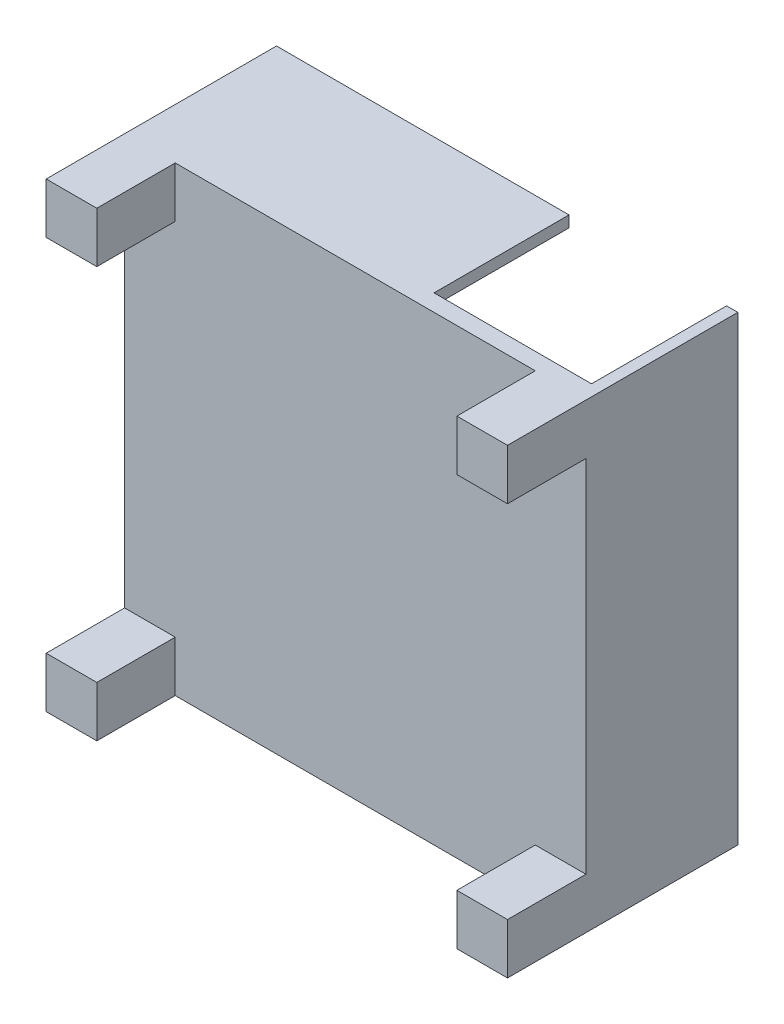
SolidWorks part; units mm, degrees
ref_plane "Piano frontale" through (0, 0, 0) normal (0, 0, 1) x (1, 0, 0)
ref_plane "Piano superiore" through (0, 0, 0) normal (0, 1, 0) x (1, 0, 0)
ref_plane "Piano destro" through (0, 0, 0) normal (1, 0, 0) x (0, 0, -1)
sketch "Schizzo1" plane through (0, 0, 0) normal (0, 0, 1) x (1, 0, 0)
  line L1 (0, 0) -> (41, 0)
  line L2 (0, 0) -> (0, 41)
  line L3 (0, 41) -> (41, 41)
  line L4 (41, 0) -> (41, 41)
  dimension "D1" = 41
  dimension "D2" = 41
extrude "Estrusione-Estrusione1" add sketch "Schizzo1" along normal blind 1.5 contours L1 L4 L3 L2
sketch "Schizzo5" plane through (0, 0, 1.5) normal (0, 0, 1) x (1, 0, 0)
  line L1 (0, 0) -> (4.5, 0)
  line L2 (0, 0) -> (0, 4.5)
  line L3 (0, 4.5) -> (4.5, 4.5)
  line L4 (4.5, 0) -> (4.5, 4.5)
  dimension "D1" = 4.5
  dimension "D2" = 4.5
extrude "Estrusione-Estrusione2" add sketch "Schizzo5" along normal blind 6.97
sketch "Schizzo6" plane through (0, 0, 1.5) normal (0, 0, 1) x (1, 0, 0)
  line L1 (41, 0) -> (36.5, 0)
  line L2 (41, 0) -> (41, 4.5)
  line L3 (41, 4.5) -> (36.5, 4.5)
  line L4 (36.5, 0) -> (36.5, 4.5)
  dimension "D1" = 4.5
  dimension "D2" = 4.5
extrude "Estrusione-Estrusione3" add sketch "Schizzo6" along normal blind 6.97
sketch "Schizzo7" plane through (0, 0, 1.5) normal (0, 0, 1) x (1, 0, 0)
  line L1 (0, 41) -> (4.5, 41)
  line L2 (0, 41) -> (0, 36.5)
  line L3 (0, 36.5) -> (4.5, 36.5)
  line L4 (4.5, 41) -> (4.5, 36.5)
  dimension "D1" = 4.5
  dimension "D2" = 4.5
extrude "Estrusione-Estrusione4" add sketch "Schizzo7" along normal blind 6.97
sketch "Schizzo8" plane through (0, 0, 1.5) normal (0, 0, 1) x (1, 0, 0)
  line L1 (41, 41) -> (36.5, 41)
  line L2 (41, 41) -> (41, 36.5)
  line L3 (41, 36.5) -> (36.5, 36.5)
  line L4 (36.5, 41) -> (36.5, 36.5)
  dimension "D1" = 4.5
  dimension "D2" = 4.5
extrude "Estrusione-Estrusione5" add sketch "Schizzo8" along normal blind 6.97
sketch "Schizzo9" plane through (0, 0, 0) normal (0, 0, -1) x (-1, 0, 0)
  line L0 (0, 0) -> (-41, 0) construction
  line L1 (-41, 41) -> (-40, 41)
  line L2 (-41, 41) -> (-41, 0)
  line L3 (-41, 0) -> (-40, 0)
  line L4 (-40, 41) -> (-40, 0)
  dimension "D1" = 1
  dimension "D2" = 41
extrude "Estrusione-Estrusione6" add sketch "Schizzo9" along normal blind 12
sketch "Schizzo10" plane through (0, 0, 0) normal (0, 0, -1) x (-1, 0, 0)
  line L0 (0, 41) -> (-40, 41) construction
  line L1 (-26, 41) -> (0, 41)
  line L2 (-26, 41) -> (-26, 40)
  line L3 (-26, 40) -> (0, 40)
  line L4 (0, 41) -> (0, 40)
  line L5 (0, 0) -> (0, 41) construction
  dimension "D1" = 26
  dimension "D2" = 1
extrude "Estrusione-Estrusione7" add sketch "Schizzo10" along normal blind 12
sketch "Schizzo11" plane through (0, 0, 8.47) normal (0, 0, 1) x (1, 0, 0)
  circle A0 centre (32.7811, 214.4993) radius 0.4
  dimension "D1" = 0.8
extrude "Taglio-Estrusione1" cut sketch "Schizzo11" against normal blind 10
sketch "Schizzo12" plane through (0, 0, 8.47) normal (0, 0, 1) x (1, 0, 0)
  circle A0 centre (-3.5189, 178.2993) radius 0.4
  dimension "D1" = 0.8
extrude "Taglio-Estrusione2" cut sketch "Schizzo12" against normal blind 10
